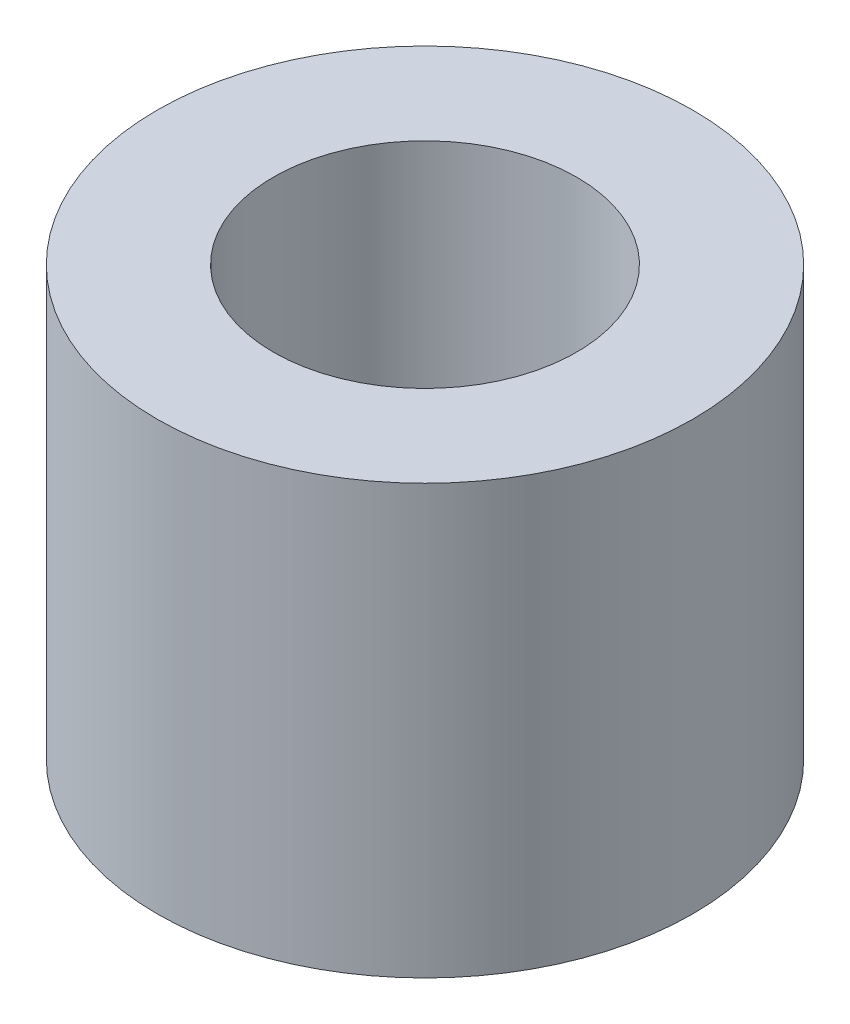
SolidWorks part; units mm, degrees
material "6061 Alloy"
ref_plane "Front Plane" through (0, 0, 0) normal (0, 0, 1) x (1, 0, 0)
ref_plane "Top Plane" through (0, 0, 0) normal (0, 1, 0) x (1, 0, 0)
ref_plane "Right Plane" through (0, 0, 0) normal (1, 0, 0) x (0, 0, -1)
sketch "Sketch1" plane through (0, 0, 0) normal (0, 1, 0) x (1, 0, 0)
  circle A0 centre (0, 0) radius 3.9688
  circle A1 centre (0, 0) radius 2.2479
  dimension "D1" = 4.4958
  dimension "D2" = 7.9375
extrude "Boss-Extrude1" add sketch "Sketch1" along normal blind 6.35
